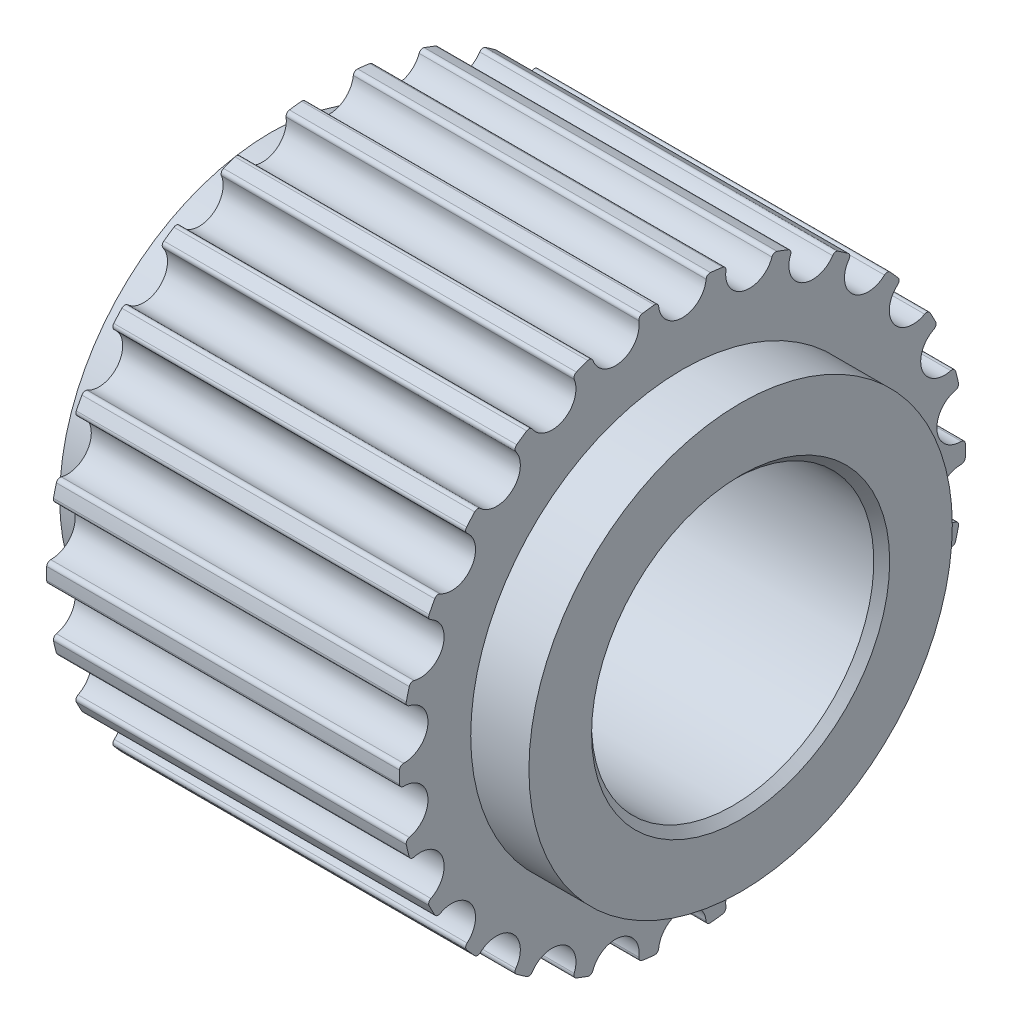
SolidWorks part; units mm, degrees
ref_plane "Front Plane" through (0, 0, 0) normal (0, 0, 1) x (1, 0, 0)
ref_plane "Top Plane" through (0, 0, 0) normal (0, 1, 0) x (1, 0, 0)
ref_plane "Right Plane" through (0, 0, 0) normal (1, 0, 0) x (0, 0, -1)
sketch "Sketch1" plane through (0, 0, 0) normal (0, 0, 1) x (1, 0, 0)
  line L2 (-6.65, 6) -> (-6.65, 4.225)
  line L3 (6.65, 4.225) -> (6.65, 6)
  line L4 (0, 0) -> (0, 10.275) construction
  line L5 (5, 8.02) -> (5, 8.7848)
  line L6 (-5, 8.02) -> (-5, 8.7848)
  line L43 (-6.425, 4) -> (6.425, 4)
  line L44 (-5, 8.275) -> (5, 8.275) construction
  line L45 (17.85, 0) -> (-17.85, 0) construction
  line L47 (-5, 7.27) -> (5, 7.27) construction
  line L48 (-5, 8.02) -> (5, 8.02)
  line L52 (-6.65, 4.225) -> (-6.425, 4)
  line L53 (-6, 8.64) -> (-6, 6)
  line L54 (-5, 6) -> (-6.65, 6)
  line L58 (6.65, 4.225) -> (6.425, 4)
  line L59 (6, 8.64) -> (6, 6)
  line L60 (5, 6) -> (6.65, 6)
  line L61 (-6.55, 10.5) -> (-6, 8.64)
  line L66 (6, 8.64) -> (6.55, 10.5)
  line L83 (5, 8.02) -> (5, 6)
  line L84 (5, 8.7848) -> (5.5072, 10.5)
  line L85 (6.55, 10.5) -> (5.5072, 10.5)
  line L86 (-5, 8.02) -> (-5, 6)
  line L87 (-5.5072, 10.5) -> (-5, 8.7848)
  line L88 (-6.55, 10.5) -> (-5.5072, 10.5)
  dimension "D5" = 0.225
  dimension "D6" = 0.225
  dimension "D7" = 12
  dimension "D8" = 10
  dimension "D9" = 13.3
  dimension "D10" = 16.04
  dimension "D11" = 21
  dimension "D12" = 1
  dimension "D13" = 1
  dimension "D14" = 17.28
  dimension "D15" = 17.5695
  dimension "D16" = 8
revolve "Revolve1" add sketch "Sketch1" angle 360 about L45
sketch "Sketch5" plane through (-5, 0, -21.5) normal (-1, 0, 0) x (0, 0, 1)
  line L1 (19, 7.6204) -> (19, 7.8883)
  line L2 (21.5, 0) -> (21.5, 19.8172) construction
  line L3 (21.5, 0) -> (2.0173, 0) construction
  line L4 (24, 7.6204) -> (24, 7.8883)
  arc A6 (22.2949, 7.9805) -> (22.1718, 7.8795) centre (22.2838, 7.8686) ccw
  arc A7 (20.8282, 7.8795) -> (22.1718, 7.8795) centre (21.5, 7.945) ccw
  arc A8 (20.8282, 7.8795) -> (20.7051, 7.9805) centre (20.7162, 7.8686) ccw
  arc A9 (24, 7.6204) -> (22.2949, 7.9805) centre (21.5, 0) ccw
  arc A10 (24, 7.8883) -> (19, 7.8883) centre (21.5, 0) ccw
  arc A11 (20.7051, 7.9805) -> (19, 7.6204) centre (21.5, 0) ccw
  circle A12 centre (21.5, 0) radius 8.02 construction
  dimension "D2" = 8.275
  dimension "D3" = 5
  dimension "D5" = 0.675
  dimension "D6" = 0.1125
  dimension "D10" = 8.02
  dimension "D7" = 1.5676
  dimension "D8" = 7.945
  dimension "D9" = 7.8686
extrude "Cut-Extrude1" cut sketch "Sketch5" against normal through all
pattern_circular "CirPattern1" count 26 over 360 about axis through (0, 0, 0) along (1, 0, 0) of "Cut-Extrude1"
